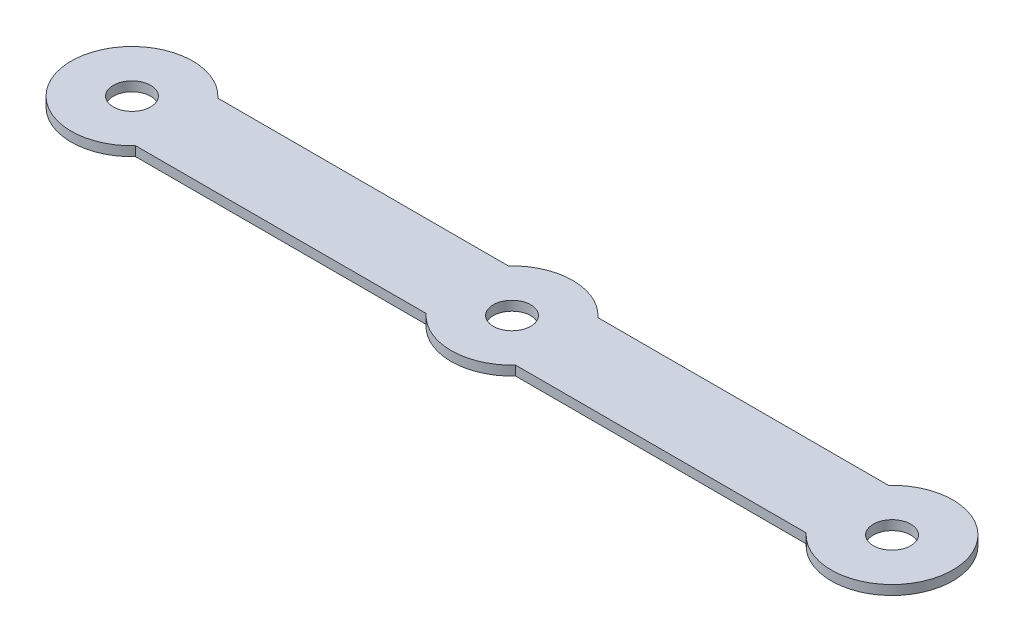
SolidWorks part; units mm, degrees
ref_plane "Front Plane" through (0, 0, 0) normal (0, 0, 1) x (1, 0, 0)
ref_plane "Top Plane" through (0, 0, 0) normal (0, 1, 0) x (1, 0, 0)
ref_plane "Right Plane" through (0, 0, 0) normal (1, 0, 0) x (0, 0, -1)
sketch "Sketch1" plane through (0, 0, 0) normal (0, 1, 0) x (1, 0, 0)
  line L0 (-89.636, 11) -> (-11.964, 11)
  line L2 (89.636, -11) -> (11.964, -11)
  line L3 (-11.964, -11) -> (-89.636, -11)
  line L4 (11.964, 11) -> (89.636, 11)
  arc A2 (-89.636, 11) -> (-89.636, -11) centre (-101.6, 0) ccw
  arc A3 (89.636, -11) -> (89.636, 11) centre (101.6, 0) ccw
  arc A4 (11.964, 11) -> (-11.964, 11) centre (0, 0) ccw
  arc A5 (-11.964, -11) -> (11.964, -11) centre (0, 0) ccw
  dimension "D1" = 32.5046
  dimension "D2" = 32.5046
  dimension "D5" = 32.5046
  dimension "D3" = 203.2
  dimension "D4" = 101.6
extrude "Boss-Extrude1" add sketch "Sketch1" along normal blind 2.54
sketch "Sketch2" plane through (0, 2.54, 0) normal (0, 1, 0) x (1, 0, 0)
  circle A0 centre (-101.6, 0) radius 5
  circle A1 centre (101.6, 0) radius 5
  circle A2 centre (0, 0) radius 5
  dimension "D2" = 10
  dimension "D4" = 10
  dimension "D5" = 10
  dimension "D1" = 101.6
  dimension "D3" = 101.6
extrude "Cut-Extrude1" cut sketch "Sketch2" against normal through all both and the other way through all
